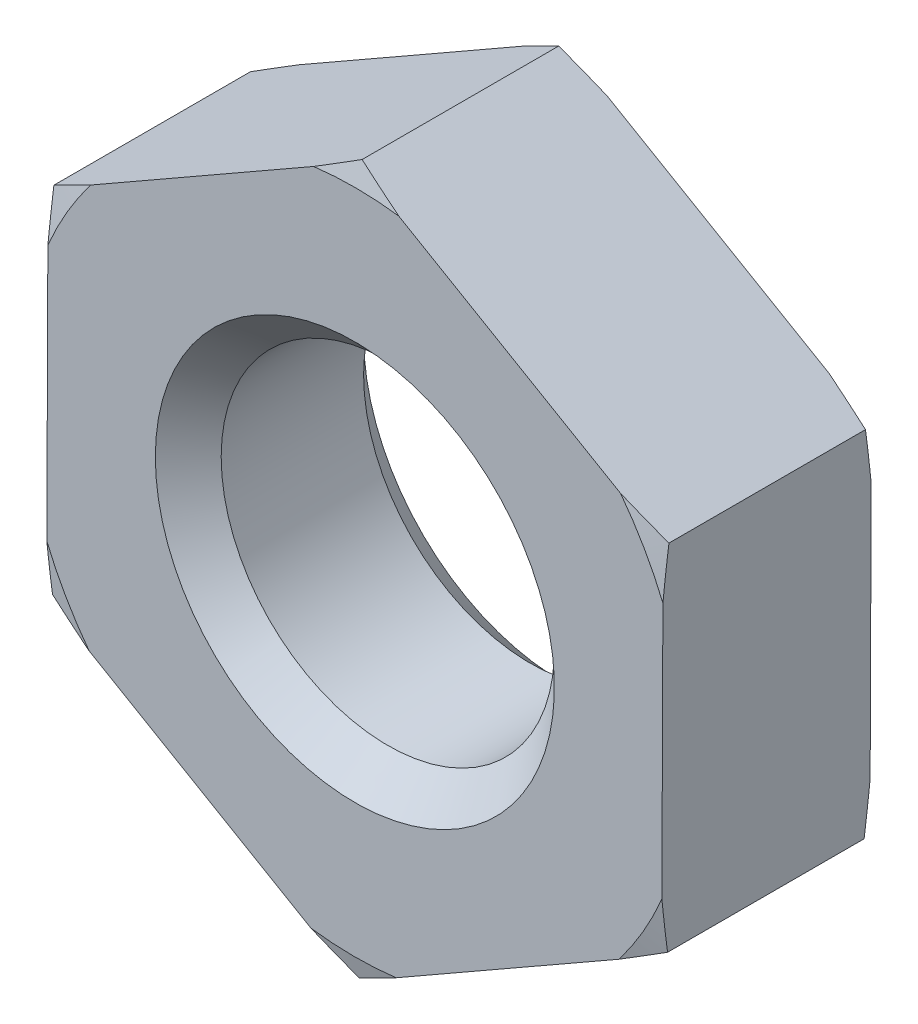
SolidWorks part; units mm, degrees
material "04级"
ref_plane "基准面1" through (0, 0, 0) normal (0, 0, 1) x (1, 0, 0)
ref_plane "基准面2" through (0, 0, 0) normal (0, 1, 0) x (1, 0, 0)
ref_plane "基准面3" through (0, 0, 0) normal (1, 0, 0) x (0, 0, -1)
sketch "尺寸草图" plane through (0, 0, 0) normal (0, 0, 1) x (1, 0, 0)
  line L0 (0, 0) -> (24.1005, 0)
  line L1 (0, 0) -> (1.84, 0)
  line L2 (46.8781, 0) -> (49.2781, 0)
  line L3 (-1.5238, 0) -> (0, 0)
  point P3 (1.6, 0)
  point P4 (2.5, 0)
  point P5 (3.41, 0)
  point P6 (1, 0)
  point P7 (7.3, 0)
  point P8 (3.2, 0)
  dimension "D1" = 1.5238
  dimension "D" = 1.6
  dimension "P" = 2.5
  dimension "e" = 3.41
  dimension "m" = 1
  dimension "mw" = 7.3
  dimension "s" = 3.2
  dimension "da" = 1.84
  dimension "dw" = 2.4
sketch "草图1" plane through (0, 0, 0) normal (0, 0, 1) x (1, 0, 0)
  line L0 (-26.8088, 0) -> (37.1748, 0) construction
  line L1 (0, 25.0215) -> (0, -25.0215) construction
  line L3 (0.0067, 1.705) -> (-1.4732, 0.8583)
  line L4 (-1.4732, 0.8583) -> (-1.4799, -0.8467)
  line L5 (-1.4799, -0.8467) -> (-0.0067, -1.705)
  line L6 (-0.0067, -1.705) -> (1.4732, -0.8583)
  line L7 (1.4732, -0.8583) -> (1.4799, 0.8467)
  line L8 (1.4799, 0.8467) -> (0.0067, 1.705)
  circle A0 centre (0, 0) radius 1.4766 construction
  circle A1 centre (0, 0) radius 0.8
  dimension "D" = 1.6
  dimension "e" = 3.41
extrude "基体-拉伸" add sketch "草图1" along normal blind 1
cosmetic thread "装饰螺纹线1"
chamfer "倒角1" distance 0.1581 angle 45 2 edges at (0.8, 0, 0) (0.8, 0, 1)
sketch "草图2" plane through (0, 0, 0) normal (0, 0, -1) x (-1, 0, 0)
  circle A0 centre (0, 0) radius 1.6
  circle A1 centre (0, 0) radius 0.8 construction
  dimension "s" = 3.2
extrude "切除-拉伸1" cut sketch "草图2" against normal through all draft 75 flip side to cut
sketch "草图3" plane through (0, 0, 1) normal (0, 0, 1) x (1, 0, 0)
  circle A0 centre (0, 0) radius 1.6
  dimension "D1" = 3.2
extrude "切除-拉伸2" cut sketch "草图3" against normal through all draft 75 flip side to cut
equation "\"e@草图1\" = \"e@尺寸草图\""
equation "\"D1@尺寸草图\" = \"D@尺寸草图\" / 1.05"
equation "\"D@草图1\" = \"D@尺寸草图\""
equation "\"m@基体-拉伸\" = \"m@尺寸草图\""
equation "\"D1@草图3\" = \"s@尺寸草图\""
equation "\"s@草图2\" = \"s@尺寸草图\""
equation "\"D2@装饰螺纹线1\" = 1.05 * \"D1@尺寸草图\""
equation "\"D1@倒角1\" =  ( \"da@尺寸草图\" - \"D1@尺寸草图\" )  / 2"
